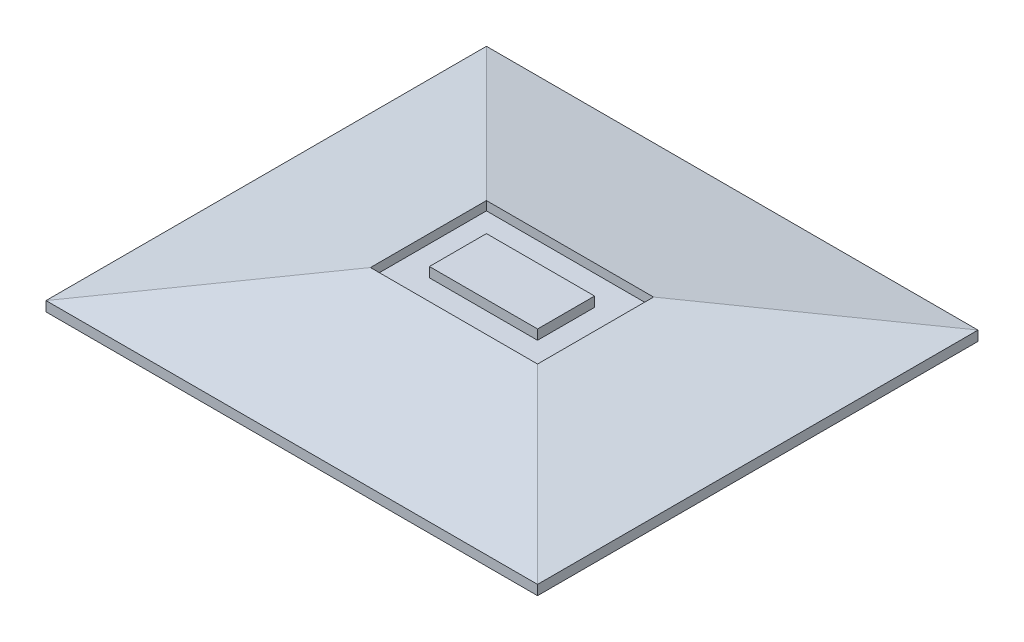
SolidWorks part; units mm, degrees
ref_plane "Front Plane" through (0, 0, 0) normal (0, 0, 1) x (1, 0, 0)
ref_plane "Top Plane" through (0, 0, 0) normal (0, 1, 0) x (1, 0, 0)
ref_plane "Right Plane" through (0, 0, 0) normal (1, 0, 0) x (0, 0, -1)
sketch "Sketch1" plane through (0, 0, 0) normal (0, 1, 0) x (1, 0, 0)
  line L1 (0, 0) -> (50, 0)
  line L2 (0, 0) -> (0, -44.8)
  line L3 (0, -44.8) -> (50, -44.8)
  line L4 (50, 0) -> (50, -44.8)
  dimension "D1" = 44.8
  dimension "D2" = 50
extrude "Boss-Extrude1" add sketch "Sketch1" along normal blind 4
sketch "Sketch2" plane through (0, 4, 0) normal (0, 1, 0) x (1, 0, 0)
  line L0 (0, -22.4) -> (50, -22.4) construction
  line L1 (16.5, -16.5) -> (33.5, -16.5)
  line L2 (16.5, -16.5) -> (16.5, -28.3)
  line L3 (16.5, -28.3) -> (33.5, -28.3)
  line L4 (33.5, -16.5) -> (33.5, -28.3)
  line L5 (19.5, -19.5) -> (30.5, -19.5)
  line L6 (19.5, -19.5) -> (19.5, -25.3)
  line L7 (19.5, -25.3) -> (30.5, -25.3)
  line L8 (30.5, -19.5) -> (30.5, -25.3)
  line L9 (0, 0) -> (0, -44.8) construction
  line L10 (50, -44.8) -> (50, 0) construction
  line L11 (25, 0) -> (25, -44.8) construction
  line L12 (50, 0) -> (0, 0) construction
  line L13 (0, -44.8) -> (50, -44.8) construction
  dimension "D2" = 3
  dimension "D3" = 3
  dimension "D5" = 5.8
  dimension "D6" = 11
chamfer "Chamfer1" distance 3 angle 80 4 edges at (50, 4, 22.4) (25, 4, 44.8) (25, 4, 0) (0, 4, 22.4)
extrude "Cut-Extrude1" cut sketch "Sketch2" against normal blind 1
sketch "Sketch3" plane through (0, 4, 0) normal (0, 1, 0) x (1, 0, 0)
  line L0 (19.5, -19.5) -> (19.5, -25.3) construction
  line L1 (19.9, -19.9) -> (30.1, -19.9)
  line L2 (19.9, -19.9) -> (19.9, -25)
  line L3 (19.9, -25) -> (30.1, -25)
  line L4 (30.1, -19.9) -> (30.1, -25)
  line L5 (30.5, -19.5) -> (19.5, -19.5) construction
  dimension "D1" = 5.1
  dimension "D2" = 10.2
  dimension "D3" = 0.4
  dimension "D4" = 0.4
extrude "Cut-Extrude2" cut sketch "Sketch3" against normal blind 3
sketch "Sketch5" plane through (0, 4, 0) normal (0, 1, 0) x (1, 0, 0)
  line L1 (19.5, -19.5) -> (30.5, -19.5)
  line L2 (19.5, -19.5) -> (19.5, -25.3)
  line L3 (19.5, -25.3) -> (30.5, -25.3)
  line L4 (30.5, -19.5) -> (30.5, -25.3)
extrude "Boss-Extrude2" add sketch "Sketch5" against normal blind 1
